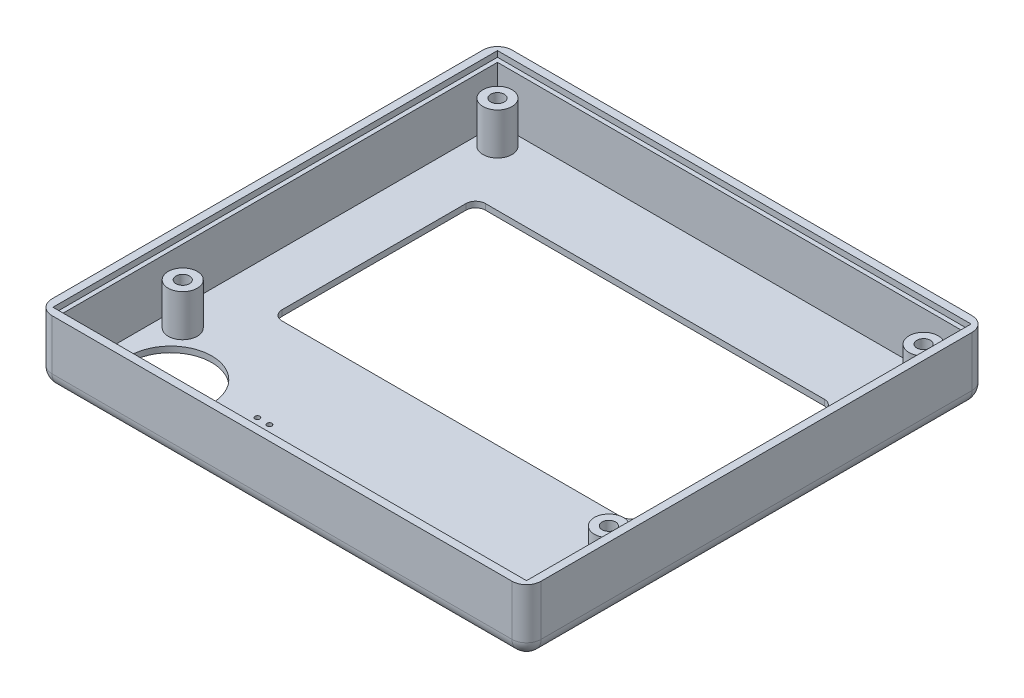
SolidWorks part; units mm, degrees
ref_plane "Front Plane" through (0, 0, 0) normal (0, 0, 1) x (1, 0, 0)
ref_plane "Top Plane" through (0, 0, 0) normal (0, 1, 0) x (1, 0, 0)
ref_plane "Right Plane" through (0, 0, 0) normal (1, 0, 0) x (0, 0, -1)
sketch "Sketch1" plane through (0, 0, 0) normal (0, 1, 0) x (1, 0, 0)
  line L1 (0, 0) -> (93, 0) construction
  line L2 (0, 0) -> (0, 87) construction
  line L3 (0, 87) -> (93, 87) construction
  line L4 (93, 0) -> (93, 87) construction
  dimension "D1" = 93
  dimension "D2" = 87
sketch "Sketch3" plane through (0, 0, 0) normal (0, 1, 0) x (1, 0, 0)
  line L8 (-4, -4) -> (97, -4)
  line L9 (97, -4) -> (97, 91)
  line L10 (-4, 91) -> (-4, -4)
  line L11 (97, 91) -> (-4, 91)
  line L12 (-4, -4) -> (97, -4)
  line L13 (97, -4) -> (97, 91)
  line L14 (-4, 91) -> (-4, -4)
  line L15 (97, 91) -> (-4, 91)
  dimension "D1" = 4
extrude "Boss-Extrude2" add sketch "Sketch3" along normal blind 1.2
sketch "Sketch5" plane through (0, 1.2, 0) normal (0, 1, 0) x (1, 0, 0)
  line L0 (-4, -4) -> (-4, 91)
  line L1 (-4, 91) -> (97, 91)
  line L2 (97, 91) -> (97, -4)
  line L3 (97, -4) -> (-4, -4)
  line L12 (-1.5, -1.5) -> (94.5, -1.5)
  line L13 (94.5, -1.5) -> (94.5, 88.5)
  line L14 (94.5, 88.5) -> (-1.5, 88.5)
  line L15 (-1.5, 88.5) -> (-1.5, -1.5)
  line L16 (-1.5, -1.5) -> (94.5, -1.5)
  line L17 (94.5, -1.5) -> (94.5, 88.5)
  line L18 (94.5, 88.5) -> (-1.5, 88.5)
  line L19 (-1.5, 88.5) -> (-1.5, -1.5)
  dimension "D1" = 1.5
extrude "Boss-Extrude3" add sketch "Sketch5" along normal blind 11
sketch "Sketch6" plane through (0, 12.2, 0) normal (0, 1, 0) x (1, 0, 0)
  line L0 (-4, -4) -> (-4, 91)
  line L1 (-4, 91) -> (97, 91)
  line L2 (97, 91) -> (97, -4)
  line L3 (97, -4) -> (-4, -4)
  line L12 (-2.4, -2.4) -> (95.4, -2.4)
  line L13 (95.4, -2.4) -> (95.4, 89.4)
  line L14 (95.4, 89.4) -> (-2.4, 89.4)
  line L15 (-2.4, 89.4) -> (-2.4, -2.4)
  line L16 (-2.4, -2.4) -> (95.4, -2.4)
  line L17 (95.4, -2.4) -> (95.4, 89.4)
  line L18 (95.4, 89.4) -> (-2.4, 89.4)
  line L19 (-2.4, 89.4) -> (-2.4, -2.4)
  dimension "D1" = 0.9
extrude "Boss-Extrude4" add sketch "Sketch6" along normal blind 1.2
fillet "Fillet1" radius 3 8 edges at (-4, 6.7, -91) (-4, 6.7, 4) (97, 6.7, -91) (97, 6.7, 4) (46.5, 0, 4) (97, 0, -43.5) (46.5, 0, -91) (-4, 0, -43.5)
sketch "Sketch7" plane through (0, 1.2, 0) normal (0, 1, 0) x (1, 0, 0)
  line L0 (0, 84.5) -> (2.5, 84.5) construction
  line L1 (0, 0) -> (0, 87) construction
  line L2 (2.5, 84.5) -> (2.5, 87) construction
  line L3 (0, 87) -> (93, 87) construction
  line L4 (90.5, 84.5) -> (93, 84.5) construction
  line L5 (93, 0) -> (93, 87) construction
  circle A0 centre (2.5, 84.5) radius 3
  circle A1 centre (90.5, 84.5) radius 3
  circle A2 centre (90.5, 19.5) radius 3
  circle A3 centre (2.5, 19.5) radius 3
  dimension "D1" = 6
  dimension "D3" = 65
  dimension "D2" = 2.5
extrude "Boss-Extrude5" add sketch "Sketch7" along normal blind 8.6
sketch "Sketch8" plane through (0, 9.8, 0) normal (0, 1, 0) x (1, 0, 0)
  circle A0 centre (2.5, 84.5) radius 1.4
  circle A1 centre (90.5, 84.5) radius 1.4
  circle A2 centre (90.5, 19.5) radius 1.4
  circle A3 centre (2.5, 19.5) radius 1.4
  dimension "D1" = 2.8
extrude "Cut-Extrude1" cut sketch "Sketch8" against normal blind 7
sketch "Sketch9" plane through (0, 1.2, 0) normal (0, 1, 0) x (1, 0, 0)
  line L0 (90.5, 84.5) -> (83.5, 73) construction
  line L1 (11.5, 31) -> (81.5, 31)
  line L2 (9.5, 33) -> (9.5, 71)
  line L3 (11.5, 73) -> (81.5, 73)
  line L4 (83.5, 33) -> (83.5, 71)
  line L6 (83.5, 31) -> (90.5, 19.5) construction
  line L7 (30, 9) -> (28.75, 11.1651) construction
  line L8 (28.75, 11.1651) -> (26.25, 11.1651) construction
  line L9 (2.5, 84.5) -> (9.5, 73) construction
  line L10 (2.5, 19.5) -> (9.5, 31) construction
  line L11 (0, 87) -> (93, 87) construction
  line L12 (0, 0) -> (0, 87) construction
  line L13 (26.25, 11.1651) -> (25, 9) construction
  line L14 (25, 9) -> (26.25, 6.8349) construction
  line L15 (26.25, 6.8349) -> (28.75, 6.8349) construction
  line L16 (28.75, 6.8349) -> (30, 9) construction
  arc A0 (11.5, 31) -> (9.5, 33) centre (11.5, 33) cw
  arc A1 (81.5, 31) -> (83.5, 33) centre (81.5, 33) ccw
  arc A2 (81.5, 73) -> (83.5, 71) centre (81.5, 71) cw
  arc A3 (9.5, 71) -> (11.5, 73) centre (11.5, 71) cw
  circle A4 centre (10.5, 9) radius 8.5
  circle A5 centre (27.5, 9) radius 0.5
  circle A6 centre (27.5, 9) radius 2.5 construction
  circle A7 centre (28.75, 11.1651) radius 0.5
  circle A8 centre (26.25, 11.1651) radius 0.5
  circle A9 centre (25, 9) radius 0.5
  circle A10 centre (26.25, 6.8349) radius 0.5
  circle A11 centre (28.75, 6.8349) radius 0.5
  circle A12 centre (30, 9) radius 0.5
  dimension "D3" = 2
  dimension "D4" = 17
  dimension "D8" = 1
  dimension "D9" = 5
  dimension "D1" = 74
  dimension "D2" = 42
  dimension "D5" = 78
  dimension "D6" = 10.5
  dimension "D7" = 17
extrude "Cut-Extrude2" cut sketch "Sketch9" against normal up to next
equation "\"D5@Sketch9\"=86.5-\"D4@Sketch9\"/2"
equation "\"D6@Sketch9\"=19-\"D4@Sketch9\"/2"
